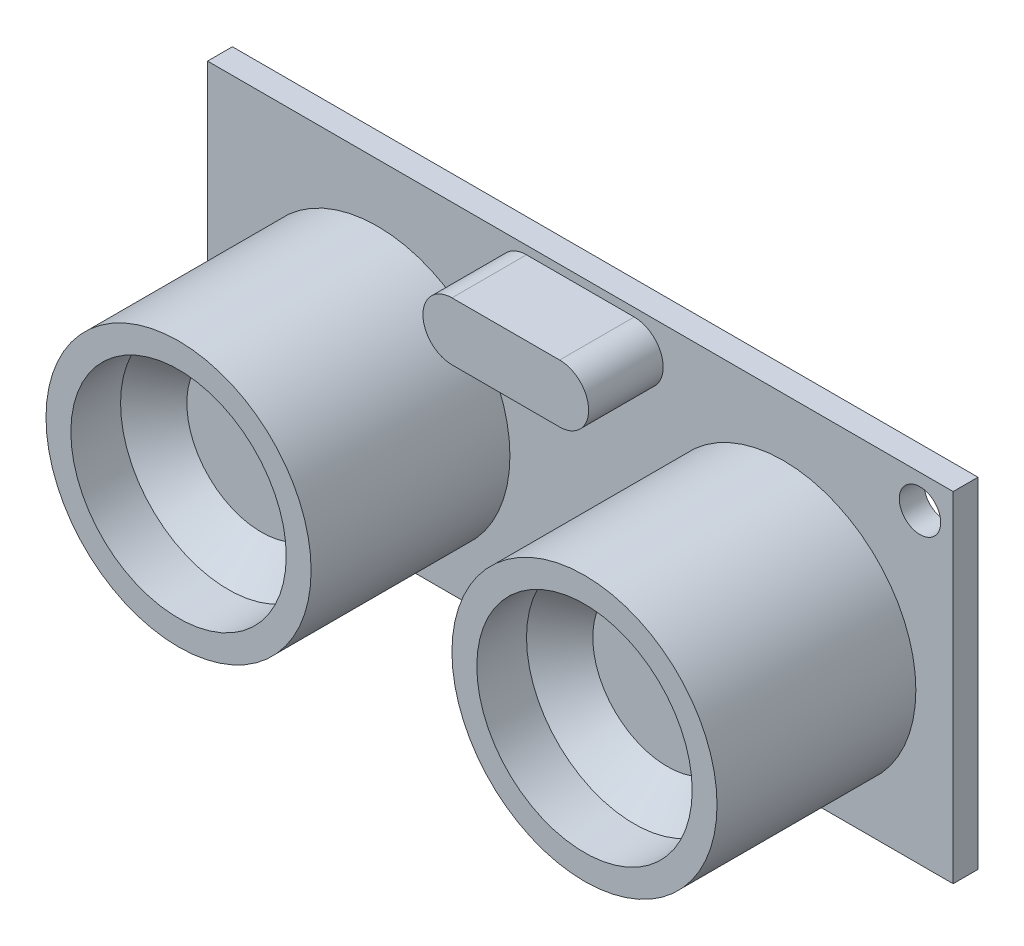
SolidWorks part; units mm, degrees
ref_plane "Front Plane" through (0, 0, 0) normal (0, 0, 1) x (1, 0, 0)
ref_plane "Top Plane" through (0, 0, 0) normal (0, 1, 0) x (1, 0, 0)
ref_plane "Right Plane" through (0, 0, 0) normal (1, 0, 0) x (0, 0, -1)
sketch "Sketch1" plane through (0, 0, 0) normal (0, 0, 1) x (1, 0, 0)
  line L0 (-22.5, -8.25) -> (-20.5, -8.25) construction
  line L1 (-22.5, 10.25) -> (22.5, 10.25)
  line L2 (-22.5, 10.25) -> (-22.5, -10.25)
  line L3 (-22.5, -10.25) -> (22.5, -10.25)
  line L4 (22.5, 10.25) -> (22.5, -10.25)
  line L5 (0, -10.25) -> (0, 10.25) construction
  line L6 (-22.5, 0) -> (22.5, 0) construction
  line L7 (-20.5, -8.25) -> (-20.5, -10.25) construction
  line L8 (20.5, 10.25) -> (20.5, 8.25) construction
  line L9 (20.5, 8.25) -> (22.5, 8.25) construction
  circle A0 centre (20.5, 8.25) radius 1.25
  circle A1 centre (-20.5, -8.25) radius 1.25
  point P0 (0, 0)
  dimension "D4" = 2.5
  dimension "D1" = 45
  dimension "D2" = 20.5
  dimension "D3" = 2
extrude "Boss-Extrude1" add sketch "Sketch1" along normal blind 1.5
sketch "Sketch2" plane through (0, 0, 1.5) normal (0, 0, 1) x (1, 0, 0)
  line L0 (0, 10.25) -> (0, -10.25) construction
  line L1 (22.5, 10.25) -> (-22.5, 10.25) construction
  line L2 (-22.5, -10.25) -> (22.5, -10.25) construction
  circle A0 centre (-12.25, -1.25) radius 8
  circle A1 centre (12.25, -1.25) radius 8
  dimension "D1" = 16
  dimension "D2" = 8.5
  dimension "D3" = 11.5
extrude "Boss-Extrude2" add sketch "Sketch2" along normal blind 12
sketch "Sketch3" plane through (0, 0, 1.5) normal (0, 0, 1) x (1, 0, 0)
  line L0 (-3.25, 8) -> (3.25, 8) construction
  line L1 (-3.25, 9.75) -> (3.25, 9.75)
  line L2 (-3.25, 6.25) -> (3.25, 6.25)
  line L3 (22.5, 10.25) -> (-22.5, 10.25) construction
  arc A0 (-3.25, 9.75) -> (-3.25, 6.25) centre (-3.25, 8) ccw
  arc A1 (3.25, 6.25) -> (3.25, 9.75) centre (3.25, 8) ccw
  point P2 (0, 8)
  point P7 (-5, 8)
  point P8 (5, 8)
  dimension "D1" = 10
  dimension "D2" = 3.5
  dimension "D3" = 0.5
extrude "Boss-Extrude3" add sketch "Sketch3" along normal blind 4.5
sketch "Sketch4" plane through (0, 0, 13.5) normal (0, 0, 1) x (1, 0, 0)
  circle A0 centre (-12.25, -1.25) radius 6.5
  dimension "D1" = 13
extrude "Cut-Extrude2" cut sketch "Sketch4" against normal blind 5
chamfer "Chamfer1" distance 2 angle 45 1 edges at (-5.75, -1.25, 8.5)
mirror "Mirror1" about plane through (0, 0, 0) normal (1, 0, 0) of "Chamfer1", "Cut-Extrude2"
sketch "Sketch5" plane through (0, 0, 0) normal (0, 0, -1) x (-1, 0, 0)
  line L0 (22.5, -10.25) -> (-22.5, -10.25) construction
  line L1 (-6.5, -7.75) -> (6.5, -7.75)
  line L2 (-6.5, -7.75) -> (-6.5, -10.25)
  line L3 (-6.5, -10.25) -> (6.5, -10.25)
  line L4 (6.5, -7.75) -> (6.5, -10.25)
  line L5 (0, -10.25) -> (0, -7.75) construction
  line L6 (-6.5, -9) -> (6.5, -9) construction
  point P0 (0, -9)
  dimension "D1" = 13
  dimension "D2" = 2.5
extrude "Boss-Extrude4" add sketch "Sketch5" along normal blind 2.5 separate body
sketch "Sketch6" plane through (0, 0, 0) normal (1, 0, 0) x (0, 0, -1)
  line L0 (2.5, -9) -> (3.5, -9)
  line L1 (2.5, -7.75) -> (2.5, -10.25) construction
  line L2 (4, -9.5) -> (4, -16.5)
  arc A0 (3.5, -9) -> (4, -9.5) centre (3.5, -9.5) cw
  point P7 (4, -9)
  dimension "D3" = 0.5
  dimension "D1" = 1.5
  dimension "D2" = 7.5
sketch "Sketch7" plane through (0, 0, -2.5) normal (0, 0, -1) x (-1, 0, 0)
  line L1 (-0.25, -8.75) -> (0.25, -8.75)
  line L2 (-0.25, -8.75) -> (-0.25, -9.25)
  line L3 (-0.25, -9.25) -> (0.25, -9.25)
  line L4 (0.25, -8.75) -> (0.25, -9.25)
  line L5 (0, -9.25) -> (0, -8.75) construction
  line L6 (-0.25, -9) -> (0.25, -9) construction
  point P0 (0, -9)
  dimension "D1" = 0.5
sweep "Sweep1" add profiles "Sketch7" path "Sketch6"
pattern_linear "LPattern1" count 3 spacing 2.5 along (-1, 0, 0) count 3 spacing 2.5 along (1, 0, 0) of "Sweep1"
